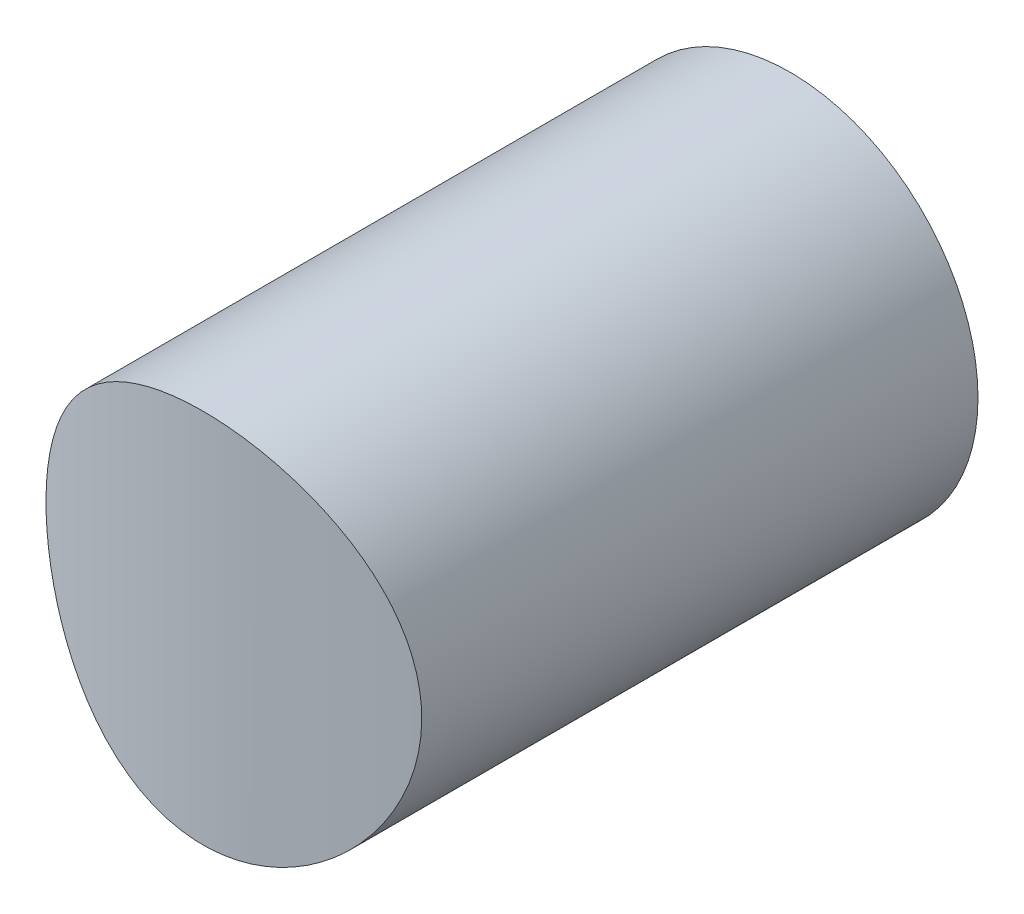
SolidWorks part; units mm, degrees
ref_plane "Front Plane" through (0, 0, 0) normal (0, 0, 1) x (1, 0, 0)
ref_plane "Top Plane" through (0, 0, 0) normal (0, 1, 0) x (1, 0, 0)
ref_plane "Right Plane" through (0, 0, 0) normal (1, 0, 0) x (0, 0, -1)
sketch "Sketch1" plane through (0, 0, 0) normal (0, 1, 0) x (1, 0, 0)
  circle A0 centre (0, 0) radius 50.8
  dimension "D1" = 101.6
extrude "Boss-Extrude1" add sketch "Sketch1" along normal blind 50.8
sketch "Sketch2" plane through (0, 0, 0) normal (0, 0, 1) x (1, 0, 0)
  line L0 (0, 50.8) -> (0, 0) construction
  line L1 (50.8, 50.8) -> (-50.8, 50.8) construction
  line L3 (-50.8, 50.8) -> (50.8, 50.8)
  line L4 (-50.8, 50.8) -> (-50.8, 0)
  line L5 (-50.8, 0) -> (50.8, 0)
  line L6 (50.8, 50.8) -> (50.8, 0)
  circle A0 centre (0, 25.4) radius 16.256
  dimension "D1" = 32.512
extrude "Cut-Extrude1" cut sketch "Sketch2" against normal through all both and the other way through all contours L0 L3 L4 L5 A0 | L3 L0 A0 L5 L6
sketch "Sketch3" plane through (0, 0, 0) normal (0, 0, 1) x (1, 0, 0)
  circle A0 centre (0, 25.4) radius 16.256
  circle A1 centre (0, 25.4) radius 16.256 construction
extrude "Cut-Extrude2" cut sketch "Sketch3" against normal through all both 50.8
sketch "Sketch4"
  dimension "D1" = 50.8
